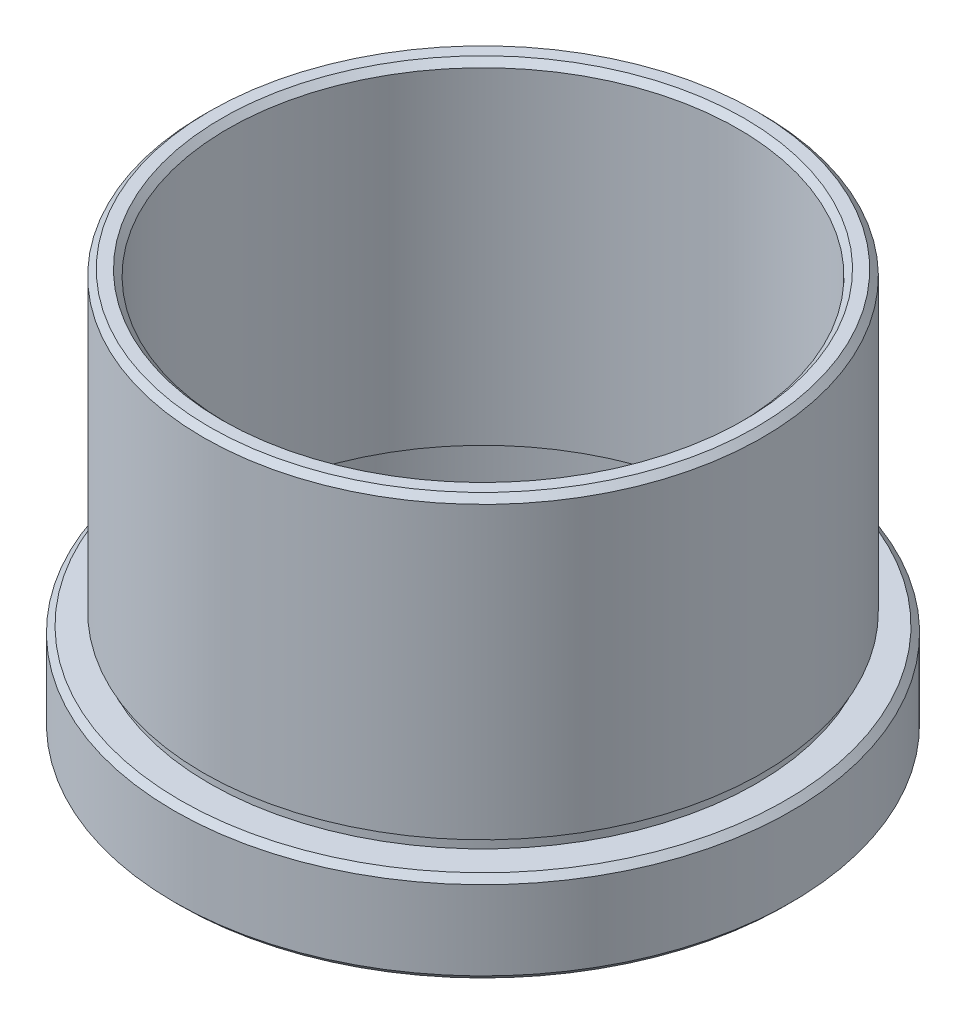
SolidWorks part; units mm, degrees
ref_plane "前视基准面" through (0, 0, 0) normal (0, 0, 1) x (1, 0, 0)
ref_plane "上视基准面" through (0, 0, 0) normal (0, 1, 0) x (1, 0, 0)
ref_plane "右视基准面" through (0, 0, 0) normal (1, 0, 0) x (0, 0, -1)
sketch "草图1" plane through (0, 0, 0) normal (0, 0, 1) x (1, 0, 0)
  line L0 (0, 44.5986) -> (0, -38.4055) construction
  line L1 (21.5, 27.0429) -> (22.5, 27.0429)
  line L2 (23, 26.5429) -> (23, 2.6429)
  line L3 (23, 2.6429) -> (22.5, 2.6429)
  line L4 (22.5, 2.6429) -> (22.5, 1.6429)
  line L5 (22.5, 1.6429) -> (24.9, 1.6429)
  line L6 (25.4, 1.1429) -> (25.4, -5.3571)
  line L7 (24.9, -5.8571) -> (24.5, -5.8571)
  line L8 (24, -5.3571) -> (24, -1.3571)
  line L9 (24, -1.3571) -> (24.1, -1.3571)
  line L10 (24.1, -1.3571) -> (24.1, -0.3571)
  line L11 (25.4, -5.3571) -> (24.9, -5.8571)
  line L12 (21, -0.3571) -> (21, 26.5429)
  line L13 (24.1, -0.3571) -> (21, -0.3571)
  line L14 (24.5, -5.8571) -> (24, -5.3571)
  line L15 (22.5, 27.0429) -> (23, 26.5429)
  line L16 (21, 26.5429) -> (21.5, 27.0429)
  line L17 (24.9, 1.6429) -> (25.4, 1.1429)
  point P3 (21, 27.0429)
  point P4 (23, 27.0429)
  point P9 (25.4, -5.8571)
  point P10 (25.4, 1.6429)
  point P11 (24, -5.8571)
  point P13 (22.5, 2.1429)
  point P14 (24.1, -0.8571)
  dimension "D2" = 25.4
  dimension "D3" = 24
  dimension "D4" = 23
  dimension "D5" = 21
  dimension "D6" = 7.5
  dimension "D7" = 5.5
  dimension "D8" = 1
  dimension "D9" = 1
  dimension "D10" = 22.5
  dimension "D11" = 24.1
revolve "旋转2" add sketch "草图1" angle 360 about L0
